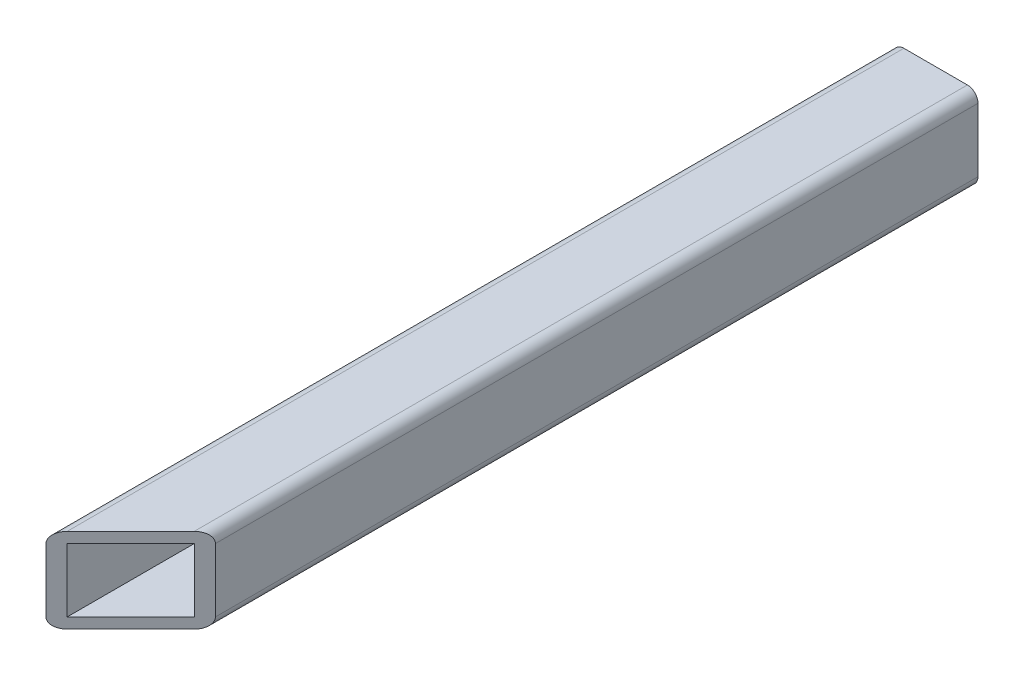
SolidWorks part; units mm, degrees
ref_plane "Front Plane" through (0, 0, 0) normal (0, 0, 1) x (1, 0, 0)
ref_plane "Top Plane" through (0, 0, 0) normal (0, 1, 0) x (1, 0, 0)
ref_plane "Right Plane" through (0, 0, 0) normal (1, 0, 0) x (0, 0, -1)
sketch "Sketch1" plane through (0, 0, 0) normal (0, 0, 1) x (1, 0, 0)
  line L1 (0, 0) -> (12.7, 0)
  line L2 (0, 0) -> (0, 12.7)
  line L3 (0, 12.7) -> (12.7, 12.7)
  line L4 (12.7, 0) -> (12.7, 12.7)
  line L5 (11.1125, 11.1125) -> (1.5875, 11.1125)
  line L6 (11.1125, 11.1125) -> (11.1125, 1.5875)
  line L7 (11.1125, 1.5875) -> (1.5875, 1.5875)
  line L8 (1.5875, 11.1125) -> (1.5875, 1.5875)
  dimension "D1" = 12.7
  dimension "D2" = 1.5875
  dimension "D3" = 1.5875
  dimension "D4" = 1.5875
extrude "Boss-Extrude1" add sketch "Sketch1" along normal blind 127
sketch "Sketch2" plane through (0, 12.7, 0) normal (0, 1, 0) x (1, 0, 0)
  line L0 (0, -127) -> (12.7, -127)
  line L1 (12.7, -127) -> (12.7, -114.3)
  line L2 (12.7, -127) -> (12.7, 0) construction
  line L3 (12.7, -114.3) -> (0, -127)
extrude "Cut-Extrude1" cut sketch "Sketch2" against normal through all
fillet "Fillet1" radius 1.5875 4 edges at (12.7, 0, 57.15) (0, 0, 63.5) (0, 12.7, 63.5) (12.7, 12.7, 57.15)
